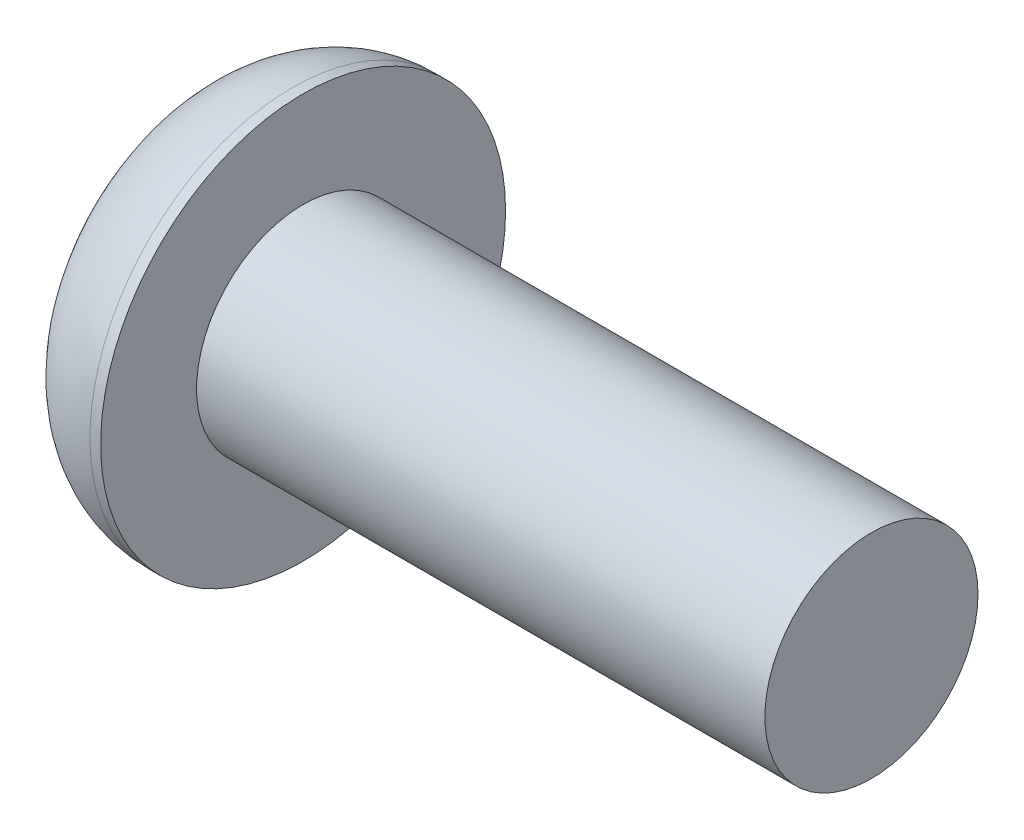
SolidWorks part; units mm, degrees
material "AISI 1020"
ref_plane "Front Plane" through (0, 0, 0) normal (0, 0, 1) x (1, 0, 0)
ref_plane "Top Plane" through (0, 0, 0) normal (0, 1, 0) x (1, 0, 0)
ref_plane "Right Plane" through (0, 0, 0) normal (1, 0, 0) x (0, 0, -1)
sketch "Sketch1" plane through (0, 0, 0) normal (0, 1, 0) x (1, 0, 0)
  line L0 (0, 0) -> (9.65, 0)
  line L1 (9.65, 0) -> (9.65, 1.5)
  line L2 (9.65, 1.5) -> (1.65, 1.5)
  line L3 (1.65, 1.5) -> (1.65, 2.85)
  line L4 (1.65, 2.85) -> (1.5, 2.85)
  line L5 (0, 1.35) -> (0, 0)
  line L6 (0, 0) -> (-8.9321, 0) construction
  arc A0 (0, 1.35) -> (1.5, 2.85) centre (1.5, 1.35) cw
  point P11 (0, 2.85)
  dimension "D5" = 1.5
  dimension "D1" = 1.5
  dimension "D2" = 8
  dimension "D3" = 1.65
  dimension "D4" = 2.85
revolve "Revolve1" add sketch "Sketch1" angle 360 about L6
sketch "Sketch2" plane through (0, 0, 0) normal (-1, 0, 0) x (0, 0, 1)
  line L1 (1.1547, 0) -> (0.5774, 1)
  line L2 (0.5774, 1) -> (-0.5774, 1)
  line L3 (-0.5774, 1) -> (-1.1547, 0)
  line L4 (-1.1547, 0) -> (-0.5774, -1)
  line L5 (-0.5774, -1) -> (0.5774, -1)
  line L6 (0.5774, -1) -> (1.1547, 0)
  circle A0 centre (0, 0) radius 1 construction
  dimension "D1" = 2
extrude "Cut-Extrude1" cut sketch "Sketch2" against normal blind 1.04
